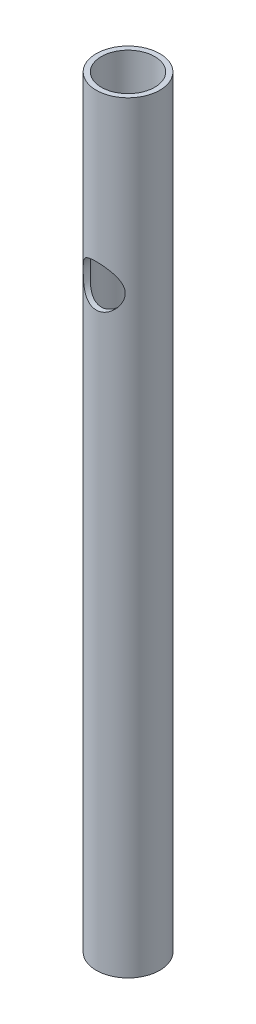
SolidWorks part; units mm, degrees
material "AISI 304"
ref_plane "Front Plane" through (0, 0, 0) normal (0, 0, 1) x (1, 0, 0)
ref_plane "Top Plane" through (0, 0, 0) normal (0, 1, 0) x (1, 0, 0)
ref_plane "Right Plane" through (0, 0, 0) normal (1, 0, 0) x (0, 0, -1)
sketch "Sketch1" plane through (0, 0, 0) normal (0, 0, 1) x (1, 0, 0)
  line L0 (0, 0) -> (0, 450) construction
  line L3 (-15.75, 450) -> (-15.75, 0)
  dimension "D1" = 15.75
  dimension "D2" = 450
revolve "Revolve-Thin1" add sketch "Sketch1" angle 360 about L0
sketch "Sketch2" plane through (0, 0, 0) normal (0, 0, 1) x (1, 0, 0)
  line L0 (18.75, 0) -> (18.75, 450) construction
  circle A0 centre (0, 350) radius 12.4
  dimension "D2" = 24.8
  dimension "D1" = 350
  dimension "D3" = 18.75
extrude "Cut-Extrude1" cut sketch "Sketch2" against normal through all and the other way through all
